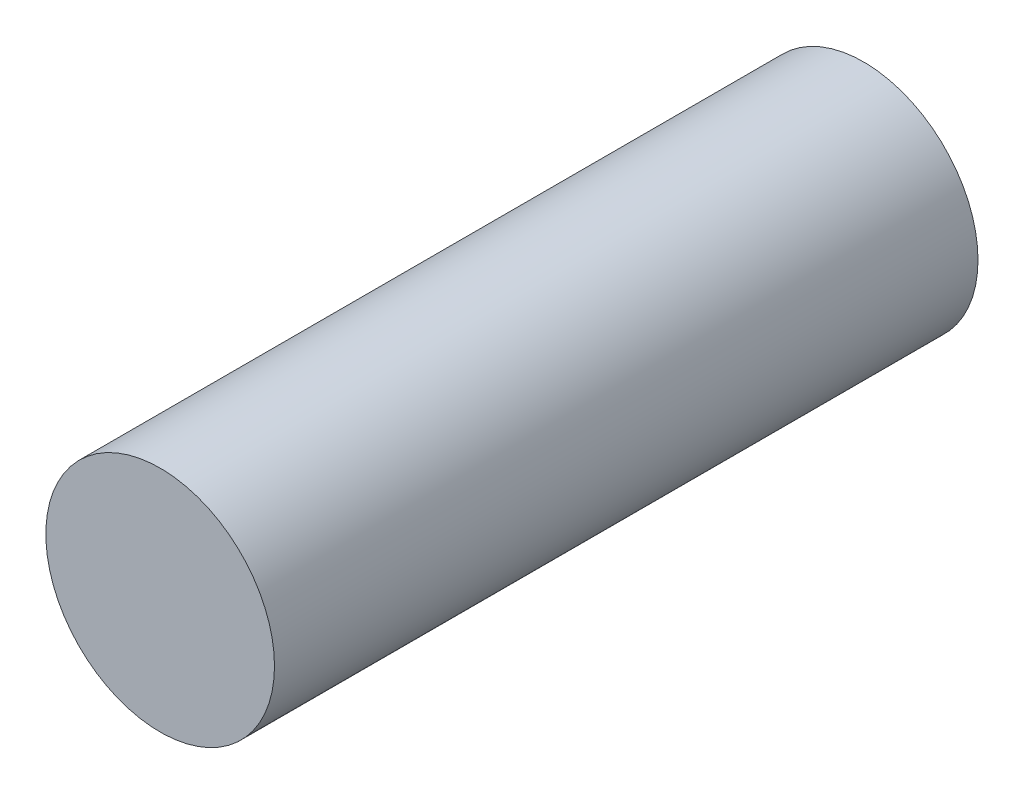
SolidWorks part; units mm, degrees
material "BUTYL"
ref_plane "Front" through (0, 0, 0) normal (0, 0, 1) x (1, 0, 0)
ref_plane "Top" through (0, 0, 0) normal (0, 1, 0) x (1, 0, 0)
ref_plane "Right" through (0, 0, 0) normal (1, 0, 0) x (0, 0, -1)
sketch "Sketch1" plane through (0, 0, 0) normal (0, 0, 1) x (1, 0, 0)
  circle A0 centre (0, 0) radius 6.5
  dimension "D1" = 13
extrude "Boss-Extrude1" add sketch "Sketch1" along normal blind 40
